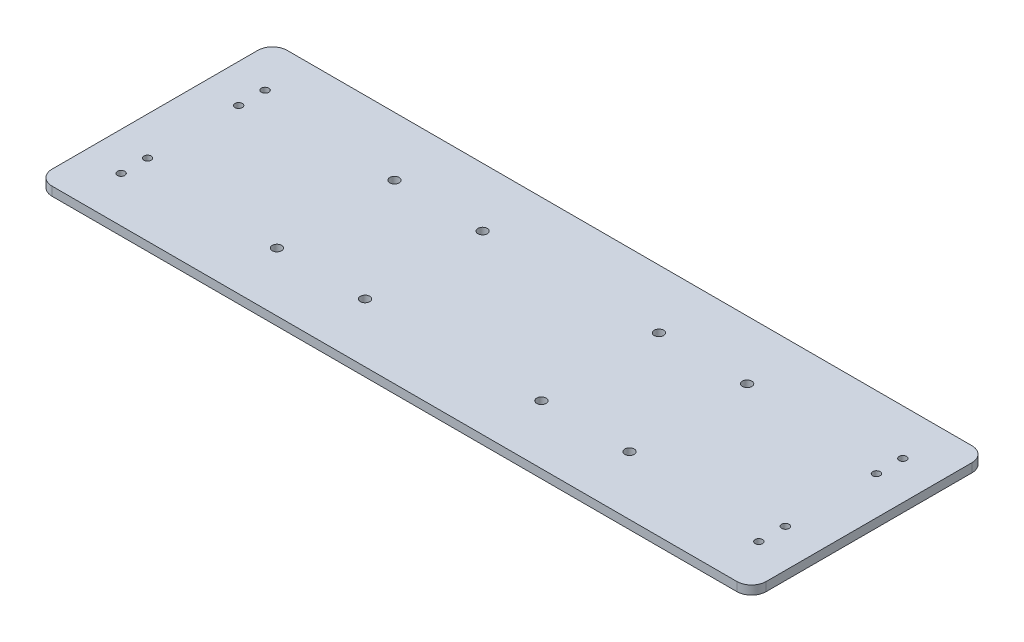
SolidWorks part; units mm, degrees
ref_plane "前视基准面" through (0, 0, 0) normal (0, 0, 1) x (1, 0, 0)
ref_plane "上视基准面" through (0, 0, 0) normal (0, 1, 0) x (1, 0, 0)
ref_plane "右视基准面" through (0, 0, 0) normal (1, 0, 0) x (0, 0, -1)
sketch "草图1" plane through (0, 0, 0) normal (0, 1, 0) x (1, 0, 0)
  line L1 (0, 0) -> (243, 0)
  line L2 (0, 0) -> (0, 80)
  line L3 (0, 80) -> (243, 80)
  line L4 (243, 0) -> (243, 80)
  dimension "D1" = 243
  dimension "D2" = 80
extrude "凸台-拉伸1" add sketch "草图1" along normal blind 3
sketch "草图2" plane through (0, 0, 0) normal (0, -1, 0) x (1, 0, 0)
  circle A0 centre (13, -64.5) radius 1.25
  circle A1 centre (13, -55.5) radius 1.25
  circle A2 centre (13, -24.5) radius 1.25
  circle A3 centre (13, -15.5) radius 1.25
  circle A4 centre (230, -55.5) radius 1.25
  circle A5 centre (230, -64.5) radius 1.25
  circle A6 centre (230, -24.5) radius 1.25
  circle A7 centre (230, -15.5) radius 1.25
extrude "切除-拉伸1" cut sketch "草图2" against normal blind 10
fillet "圆角1" radius 5 4 edges at (243, 1.5, 0) (243, 1.5, -80) (0, 1.5, 0) (0, 1.5, -80)
sketch "草图3" plane through (0, 0, 0) normal (0, -1, 0) x (1, 0, 0)
  line L0 (121.5, 0) -> (121.5, -122.1744) construction
  line L1 (5, 0) -> (238, 0) construction
  line L2 (0, -40) -> (305.0012, -40) construction
  line L3 (0, -75) -> (0, -5) construction
  circle A0 centre (61.5, -20) radius 1.6
  circle A1 centre (91.5, -20) radius 1.6
  circle A2 centre (151.5, -20) radius 1.6
  circle A3 centre (181.5, -20) radius 1.6
  circle A4 centre (181.5, -60) radius 1.6
  circle A5 centre (151.5, -60) radius 1.6
  circle A6 centre (91.5, -60) radius 1.6
  circle A7 centre (61.5, -60) radius 1.6
  dimension "D1" = 3.2
  dimension "D2" = 3.2
  dimension "D3" = 30
  dimension "D4" = 60
  dimension "D5" = 20
  dimension "D6" = 20
extrude "切除-拉伸2" cut sketch "草图3" against normal blind 10
